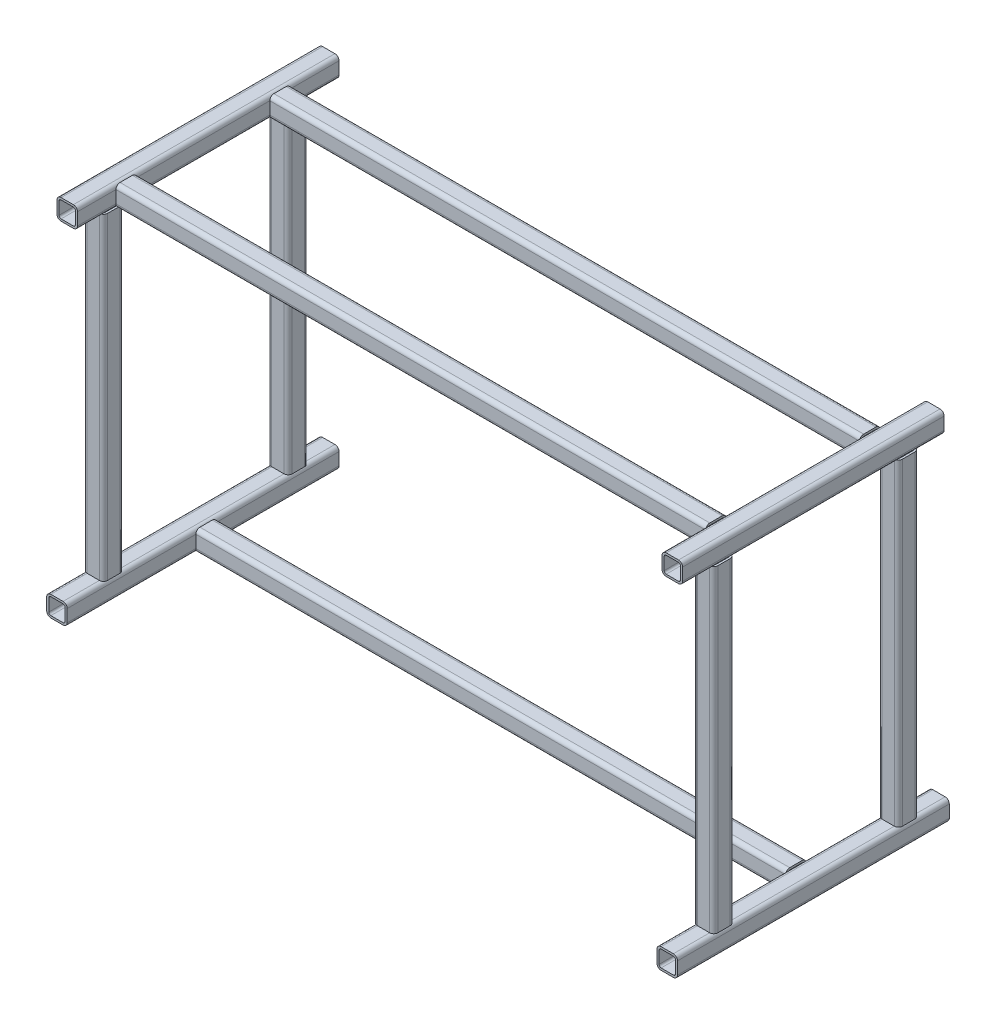
SolidWorks part; units mm, degrees
ref_plane "Front Plane" through (0, 0, 0) normal (0, 0, 1) x (1, 0, 0)
ref_plane "Top Plane" through (0, 0, 0) normal (0, 1, 0) x (1, 0, 0)
ref_plane "Right Plane" through (0, 0, 0) normal (1, 0, 0) x (0, 0, -1)
sketch "Croquis1" plane through (0, 0, 0) normal (0, 1, 0) x (1, 0, 0)
  line L0 (-595, 0) -> (595, 0)
  line L1 (-595, 259.214) -> (-595, -270.786)
  line L2 (595, 259.214) -> (595, -270.786)
  point P7 (0, 0)
  dimension "D1" = 530
  dimension "D2" = 530
  dimension "D3" = 1190
other "Tubo cuadrado 40 X 40 X 4(1)"
ref_plane "Plano1" through (-595, 0, -259.214) normal (0, 0, 1) x (1, 0, 0)
sketch "Sketch1" plane through (-595, 0, -259.214) normal (0, 0, 1) x (1, 0, 0)
  line L0 (-12, -16) -> (12, -16)
  line L1 (-16, -12) -> (-16, 12)
  line L2 (12, 16) -> (-12, 16)
  line L3 (16, 12) -> (16, -12)
  line L4 (-12, -20) -> (12, -20)
  line L5 (-20, -12) -> (-20, 12)
  line L6 (12, 20) -> (-12, 20)
  line L7 (20, 12) -> (20, -12)
  arc A0 (20, 12) -> (12, 20) centre (12, 12) ccw
  arc A1 (12, -20) -> (20, -12) centre (12, -12) ccw
  arc A2 (-20, -12) -> (-12, -20) centre (-12, -12) ccw
  arc A3 (-12, 20) -> (-20, 12) centre (-12, 12) ccw
  arc A4 (-12, 16) -> (-16, 12) centre (-12, 12) ccw
  arc A5 (16, 12) -> (12, 16) centre (12, 12) ccw
  arc A6 (12, -16) -> (16, -12) centre (12, -12) ccw
  arc A7 (-16, -12) -> (-12, -16) centre (-12, -12) ccw
  point P0 (-20, 0)
  point P1 (20, 0)
  point P2 (0, 20)
  point P3 (0, -20)
  point P4 (0, 0)
  point P5 (-20, -20)
  point P6 (20, -20)
  point P7 (20, 20)
  point P8 (-20, 20)
  point P33 (0, 0)
  dimension "D1" = 8
  dimension "Thickness" = 4
  dimension "V_leg" = 40
ref_plane "Plano3" through (595, 0, 0) normal (1, 0, 0) x (0, 0, -1)
sketch "Croquis4" plane through (595, 0, 0) normal (1, 0, 0) x (0, 0, -1)
  line L0 (0, 0) -> (0, 20) construction
  line L1 (0, 20) -> (-180, 20) construction
  line L2 (0, 20) -> (180, 20) construction
  line L3 (-180, 20) -> (-180, 640)
  line L4 (180, 20) -> (180, 640)
  dimension "D1" = 20
  dimension "D2" = 180
  dimension "D3" = 180
  dimension "D4" = 620
  dimension "D5" = 620
  dimension "D6" = 20
other "Tubo cuadrado 40 X 40 X 4(2)"
ref_plane "Plano4" through (595, 20, 180) normal (0, 1, 0) x (0, 0, 1)
sketch "Sketch11" plane through (595, 20, 180) normal (0, 1, 0) x (0, 0, 1)
  line L0 (-12, -16) -> (12, -16)
  line L1 (-16, -12) -> (-16, 12)
  line L2 (12, 16) -> (-12, 16)
  line L3 (16, 12) -> (16, -12)
  line L4 (-12, -20) -> (12, -20)
  line L5 (-20, -12) -> (-20, 12)
  line L6 (12, 20) -> (-12, 20)
  line L7 (20, 12) -> (20, -12)
  arc A0 (20, 12) -> (12, 20) centre (12, 12) ccw
  arc A1 (12, -20) -> (20, -12) centre (12, -12) ccw
  arc A2 (-20, -12) -> (-12, -20) centre (-12, -12) ccw
  arc A3 (-12, 20) -> (-20, 12) centre (-12, 12) ccw
  arc A4 (-12, 16) -> (-16, 12) centre (-12, 12) ccw
  arc A5 (16, 12) -> (12, 16) centre (12, 12) ccw
  arc A6 (12, -16) -> (16, -12) centre (12, -12) ccw
  arc A7 (-16, -12) -> (-12, -16) centre (-12, -12) ccw
  point P0 (-20, 0)
  point P1 (20, 0)
  point P2 (0, 20)
  point P3 (0, -20)
  point P4 (0, 0)
  point P5 (-20, -20)
  point P6 (20, -20)
  point P7 (20, 20)
  point P8 (-20, 20)
  point P33 (0, 0)
  dimension "D1" = 8
  dimension "Thickness" = 4
  dimension "V_leg" = 40
ref_plane "Plano5" through (-595, 0, 0) normal (1, 0, 0) x (0, 0, -1)
sketch "Croquis6" plane through (-595, 0, -575) normal (1, 0, 0) x (0, 0, -1)
  line L0 (-575, 0) -> (-575, 20) construction
  line L1 (-575, 20) -> (-755, 20) construction
  line L2 (-575, 20) -> (-395, 20) construction
  line L3 (-755, 20) -> (-755, 640)
  line L4 (-395, 20) -> (-395, 640)
  dimension "D1" = 20
  dimension "D2" = 180
  dimension "D3" = 180
  dimension "D4" = 620
  dimension "D5" = 620
  dimension "D6" = 20
other "Tubo cuadrado 40 X 40 X 4(3)"
ref_plane "Plano6" through (-595, 20, 180) normal (0, 1, 0) x (0, 0, 1)
sketch "Sketch12" plane through (-595, 20, 180) normal (0, 1, 0) x (0, 0, 1)
  line L0 (-12, -16) -> (12, -16)
  line L1 (-16, -12) -> (-16, 12)
  line L2 (12, 16) -> (-12, 16)
  line L3 (16, 12) -> (16, -12)
  line L4 (-12, -20) -> (12, -20)
  line L5 (-20, -12) -> (-20, 12)
  line L6 (12, 20) -> (-12, 20)
  line L7 (20, 12) -> (20, -12)
  arc A0 (20, 12) -> (12, 20) centre (12, 12) ccw
  arc A1 (12, -20) -> (20, -12) centre (12, -12) ccw
  arc A2 (-20, -12) -> (-12, -20) centre (-12, -12) ccw
  arc A3 (-12, 20) -> (-20, 12) centre (-12, 12) ccw
  arc A4 (-12, 16) -> (-16, 12) centre (-12, 12) ccw
  arc A5 (16, 12) -> (12, 16) centre (12, 12) ccw
  arc A6 (12, -16) -> (16, -12) centre (12, -12) ccw
  arc A7 (-16, -12) -> (-12, -16) centre (-12, -12) ccw
  point P0 (-20, 0)
  point P1 (20, 0)
  point P2 (0, 20)
  point P3 (0, -20)
  point P4 (0, 0)
  point P5 (-20, -20)
  point P6 (20, -20)
  point P7 (20, 20)
  point P8 (-20, 20)
  point P33 (0, 0)
  dimension "D1" = 8
  dimension "Thickness" = 4
  dimension "V_leg" = 40
ref_plane "Plano7" through (0, 660, 0) normal (0, 1, 0) x (1, 0, 0)
sketch "Croquis8" plane through (0, 660, -660) normal (0, -1, 0) x (1, 0, 0)
  line L0 (-595, 665.786) -> (595, 665.786)
  line L1 (-595, 910.786) -> (-595, 400.786)
  line L2 (595, 920.786) -> (595, 410.786)
  line L3 (595, 815.786) -> (-595, 815.786)
  line L4 (595, 515.786) -> (-595, 515.786)
  line L6 (-607, 930.786) -> (-607, 400.786) construction
  point P10 (595, 665.786)
  point P14 (-607, 665.786)
  dimension "D1" = 510
  dimension "D2" = 510
  dimension "D3" = 1190
  dimension "D4" = 150
  dimension "D5" = 150
other "Tubo cuadrado 40 X 40 X 4(5)"
ref_plane "Plano9" through (595, 660, 260.786) normal (0, 0, -1) x (-1, 0, 0)
sketch "Sketch14" plane through (595, 660, 260.786) normal (0, 0, -1) x (-1, 0, 0)
  line L0 (-12, -16) -> (12, -16)
  line L1 (-16, -12) -> (-16, 12)
  line L2 (12, 16) -> (-12, 16)
  line L3 (16, 12) -> (16, -12)
  line L4 (-12, -20) -> (12, -20)
  line L5 (-20, -12) -> (-20, 12)
  line L6 (12, 20) -> (-12, 20)
  line L7 (20, 12) -> (20, -12)
  arc A0 (20, 12) -> (12, 20) centre (12, 12) ccw
  arc A1 (12, -20) -> (20, -12) centre (12, -12) ccw
  arc A2 (-20, -12) -> (-12, -20) centre (-12, -12) ccw
  arc A3 (-12, 20) -> (-20, 12) centre (-12, 12) ccw
  arc A4 (-12, 16) -> (-16, 12) centre (-12, 12) ccw
  arc A5 (16, 12) -> (12, 16) centre (12, 12) ccw
  arc A6 (12, -16) -> (16, -12) centre (12, -12) ccw
  arc A7 (-16, -12) -> (-12, -16) centre (-12, -12) ccw
  point P0 (-20, 0)
  point P1 (20, 0)
  point P2 (0, 20)
  point P3 (0, -20)
  point P4 (0, 0)
  point P5 (-20, -20)
  point P6 (20, -20)
  point P7 (20, 20)
  point P8 (-20, 20)
  point P33 (0, 0)
  dimension "D1" = 8
  dimension "Thickness" = 4
  dimension "V_leg" = 40
